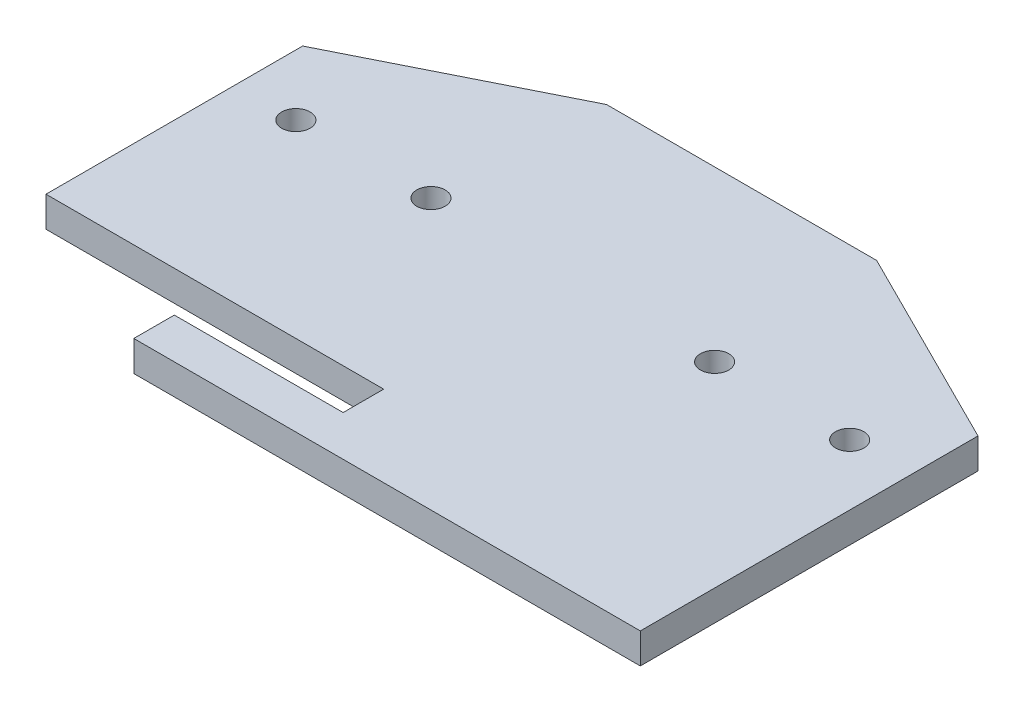
SolidWorks part; units mm, degrees
ref_plane "Front Plane" through (0, 0, 0) normal (0, 0, 1) x (1, 0, 0)
ref_plane "Top Plane" through (0, 0, 0) normal (0, 1, 0) x (1, 0, 0)
ref_plane "Right Plane" through (0, 0, 0) normal (1, 0, 0) x (0, 0, -1)
sketch "Sketch1" plane through (0, 0, 0) normal (0, 1, 0) x (1, 0, 0)
  line L0 (20, 40) -> (50, 25)
  line L1 (-20, 40) -> (-50, 25)
  line L2 (-50, 25) -> (-50, -25)
  line L3 (-50, -25) -> (50, -25)
  line L4 (50, 25) -> (50, -25)
  line L5 (-50, 25) -> (50, -25) construction
  line L6 (-50, -25) -> (50, 25) construction
  line L7 (0, 40) -> (20, 40)
  line L8 (0, 40) -> (-20, 40)
  circle A0 centre (-41, 15) radius 2.1
  circle A1 centre (41, 15) radius 2.1
  circle A2 centre (-21, 15) radius 2.1
  circle A3 centre (21, 15) radius 2.1
  point P0 (0, 0)
  dimension "D3" = 4.2
  dimension "D4" = 4.2
  dimension "D6" = 20
  dimension "D7" = 4.2
  dimension "D8" = 4.2
  dimension "D1" = 100
  dimension "D2" = 50
  dimension "D5" = 82
  dimension "D9" = 20
  dimension "D10" = 15
  dimension "D11" = 21
  dimension "D12" = 20
  dimension "D13" = 20
extrude "Boss-Extrude1" add sketch "Sketch1" along normal blind 4.5
sketch "Sketch2" plane through (0, 4.5, 0) normal (0, 1, 0) x (1, 0, 0)
  line L0 (-50, 25) -> (-50, -25) construction
  line L1 (-50, -19) -> (-50, -25)
  line L2 (-50, -19) -> (-50, -13)
  line L3 (-50, -13) -> (0, -13)
  line L4 (0, -19) -> (0, -13)
  line L6 (-50, -25) -> (-25, -25)
  line L7 (-50, -25) -> (50, -25) construction
  line L8 (-25, -25) -> (-25, -19)
  line L9 (-25, -19) -> (0, -19)
  dimension "D1" = 25
  dimension "D2" = 6
  dimension "D3" = 50
extrude "Cut-Extrude1" cut sketch "Sketch2" against normal blind 10
